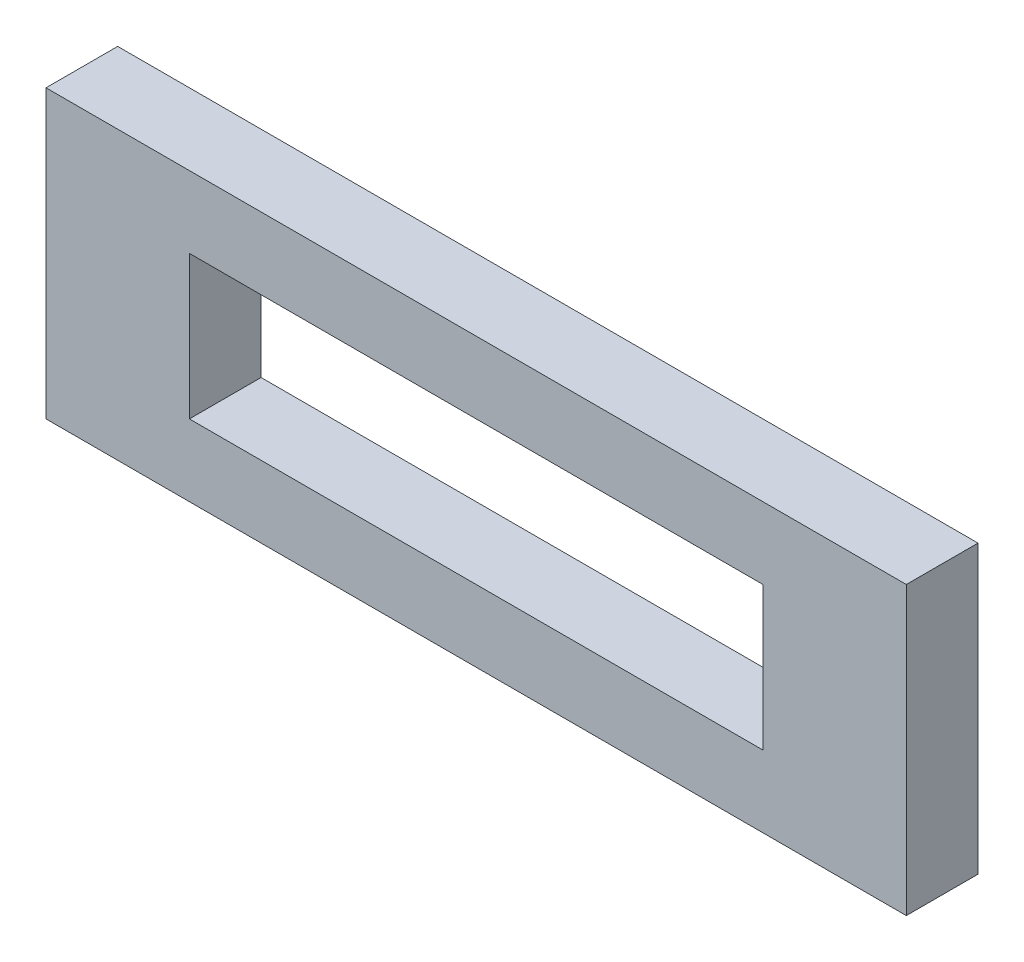
SolidWorks part; units mm, degrees
ref_plane "Front Plane" through (0, 0, 0) normal (0, 0, 1) x (1, 0, 0)
ref_plane "Top Plane" through (0, 0, 0) normal (0, 1, 0) x (1, 0, 0)
ref_plane "Right Plane" through (0, 0, 0) normal (1, 0, 0) x (0, 0, -1)
sketch "Sketch1" plane through (0, 0, 0) normal (0, 0, 1) x (1, 0, 0)
  line L1 (-19.05, 6.35) -> (19.05, 6.35)
  line L2 (-19.05, 6.35) -> (-19.05, -6.35)
  line L3 (-19.05, -6.35) -> (19.05, -6.35)
  line L4 (19.05, 6.35) -> (19.05, -6.35)
  line L5 (-12.7, 3.175) -> (12.7, 3.175)
  line L6 (-12.7, 3.175) -> (-12.7, -3.175)
  line L7 (-12.7, -3.175) -> (12.7, -3.175)
  line L8 (12.7, 3.175) -> (12.7, -3.175)
  dimension "D5" = 25.4
  dimension "D1" = 38.1
  dimension "D2" = 19.05
  dimension "D3" = 12.7
  dimension "D4" = 6.35
  dimension "D6" = 6.35
  dimension "D7" = 3.175
  dimension "D8" = 12.7
extrude "Extrude1" add sketch "Sketch1" along normal blind 3.175
equation "\"D2@Sketch1\" = \"D1@Sketch1\" / 2"
equation "\"D4@Sketch1\" = \"D3@Sketch1\" / 2"
equation "\"D7@Sketch1\" = \"D6@Sketch1\" / 2"
equation "\"D8@Sketch1\" = \"D5@Sketch1\" / 2"
